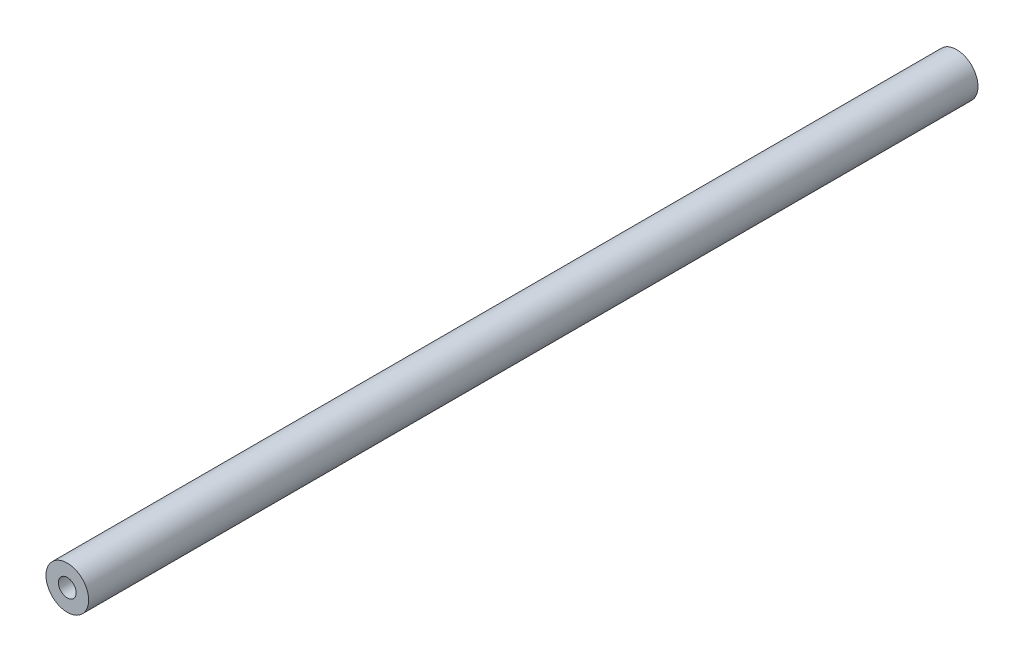
SolidWorks part; units mm, degrees
ref_plane "Alzado" through (0, 0, 0) normal (0, 0, 1) x (1, 0, 0)
ref_plane "Planta" through (0, 0, 0) normal (0, 1, 0) x (1, 0, 0)
ref_plane "Vista lateral" through (0, 0, 0) normal (1, 0, 0) x (0, 0, -1)
sketch "Croquis1" plane through (0, 0, 0) normal (0, 0, 1) x (1, 0, 0)
  circle A0 centre (0, 0) radius 6
extrude "Saliente-Extruir1" add sketch "Croquis1" along normal blind 250
sketch "Croquis2" plane through (0, 0, 250) normal (0, 0, 1) x (1, 0, 0)
  circle A0 centre (0, 0) radius 2.5
extrude "Cortar-Extruir1" cut sketch "Croquis2" against normal blind 15
sketch "Croquis3" plane through (0, 0, 0) normal (0, 0, -1) x (-1, 0, 0)
  circle A0 centre (0, 0) radius 2.5
extrude "Cortar-Extruir2" cut sketch "Croquis3" against normal blind 15
